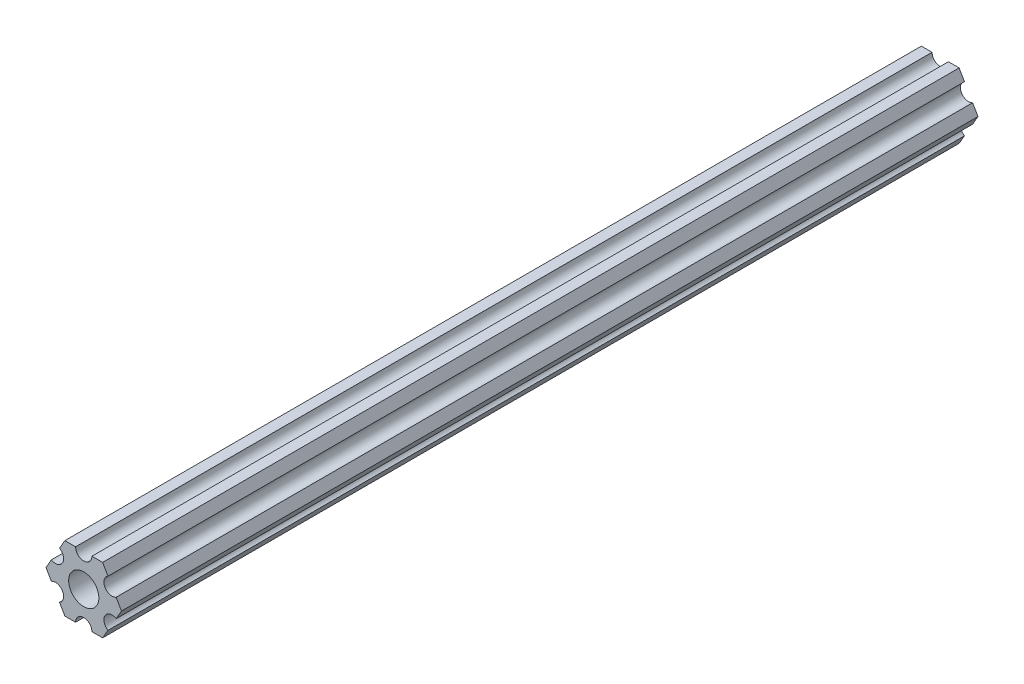
SolidWorks part; units mm, degrees
ref_plane "Front" through (0, 0, 0) normal (0, 0, 1) x (1, 0, 0)
ref_plane "Top" through (0, 0, 0) normal (0, 1, 0) x (1, 0, 0)
ref_plane "Right" through (0, 0, 0) normal (1, 0, 0) x (0, 0, -1)
ref_plane "Plane1" through (0, 0, 0) normal (0, 0, -1) x (-1, 0, 0)
sketch "Sketch1" plane through (0, 0, 0) normal (0, 0, -1) x (-1, 0, 0)
  line L0 (-4.7055, -4.5498) -> (-3.6662, -6.35)
  line L1 (-3.6662, -6.35) -> (-1.5875, -6.35)
  line L2 (1.5875, -6.35) -> (3.6662, -6.35)
  line L3 (3.6662, -6.35) -> (4.7055, -4.5498)
  line L4 (6.293, -1.8002) -> (7.3323, 0)
  line L5 (7.3323, 0) -> (6.293, 1.8002)
  line L6 (4.7055, 4.5498) -> (3.6662, 6.35)
  line L7 (3.6662, 6.35) -> (1.5875, 6.35)
  line L8 (-1.5875, 6.35) -> (-3.6662, 6.35)
  line L9 (-3.6662, 6.35) -> (-4.7055, 4.5498)
  line L10 (-6.293, 1.8002) -> (-7.3323, 0)
  line L11 (-7.3323, 0) -> (-6.293, -1.8002)
  circle A0 centre (0, 0) radius 2.9337
  arc A1 (-6.293, -1.8002) -> (-4.7055, -4.5498) centre (-5.4993, -3.175) cw
  arc A2 (-1.5875, -6.35) -> (1.5875, -6.35) centre (0, -6.35) cw
  arc A3 (4.7055, -4.5498) -> (6.293, -1.8002) centre (5.4993, -3.175) cw
  arc A4 (6.293, 1.8002) -> (4.7055, 4.5498) centre (5.4993, 3.175) cw
  arc A5 (1.5875, 6.35) -> (-1.5875, 6.35) centre (0, 6.35) cw
  arc A6 (-4.7055, 4.5498) -> (-6.293, 1.8002) centre (-5.4993, 3.175) cw
extrude "Boss-Extrude1" add sketch "Sketch1" against normal blind 166.37
